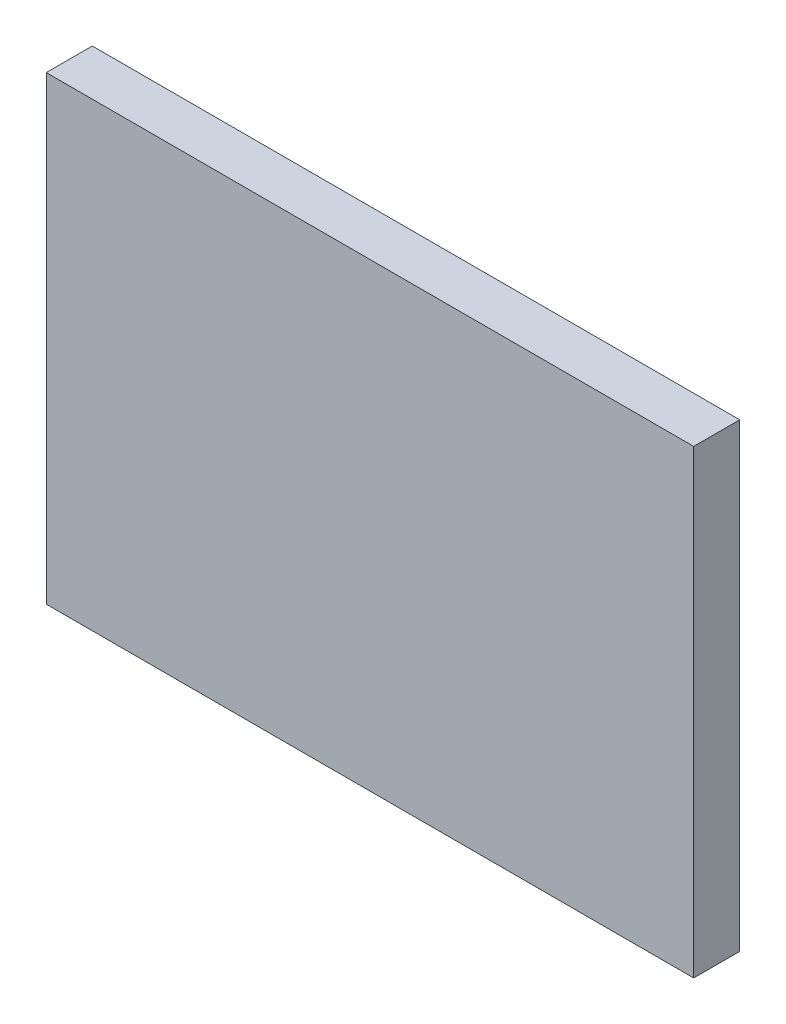
SolidWorks part; units mm, degrees
material "Epoxy, Unfilled"
ref_plane "Front Plane" through (0, 0, 0) normal (0, 0, 1) x (1, 0, 0)
ref_plane "Top Plane" through (0, 0, 0) normal (0, 1, 0) x (1, 0, 0)
ref_plane "Right Plane" through (0, 0, 0) normal (1, 0, 0) x (0, 0, -1)
sketch "Sketch1" plane through (0, 0, 0) normal (0, 0, 1) x (1, 0, 0)
  line L1 (-11.25, 8) -> (11.25, 8)
  line L2 (-11.25, 8) -> (-11.25, -8)
  line L3 (-11.25, -8) -> (11.25, -8)
  line L4 (11.25, 8) -> (11.25, -8)
  line L5 (-11.25, 8) -> (11.25, -8) construction
  line L6 (-11.25, -8) -> (11.25, 8) construction
  point P0 (0, 0)
  dimension "D1" = 22.5
  dimension "D2" = 16
extrude "Boss-Extrude1" add sketch "Sketch1" along normal blind 1.6
